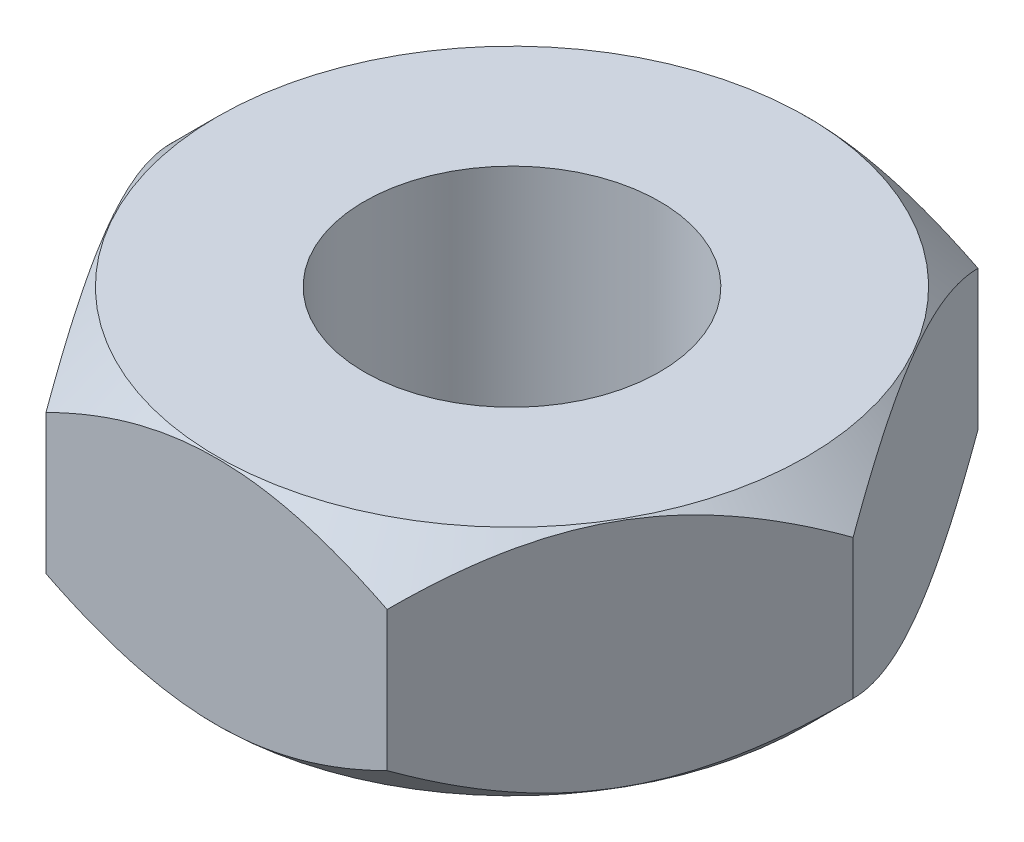
SolidWorks part; units mm, degrees
ref_plane "Alzado" through (0, 0, 0) normal (0, 0, 1) x (1, 0, 0)
ref_plane "Planta" through (0, 0, 0) normal (0, 1, 0) x (1, 0, 0)
ref_plane "Vista lateral" through (0, 0, 0) normal (1, 0, 0) x (0, 0, -1)
sketch "Croquis1" plane through (0, 0, 0) normal (0, 1, 0) x (1, 0, 0)
  line L1 (-7.3323, -12.7) -> (7.3323, -12.7)
  line L2 (7.3323, -12.7) -> (14.6647, 0)
  line L3 (14.6647, 0) -> (7.3323, 12.7)
  line L4 (7.3323, 12.7) -> (-7.3323, 12.7)
  line L5 (-7.3323, 12.7) -> (-14.6647, 0)
  line L6 (-14.6647, 0) -> (-7.3323, -12.7)
  circle A0 centre (0, 0) radius 12.7 construction
  circle A1 centre (0, 0) radius 6.35
  dimension "D2" = 12.7
  dimension "D1" = 25.4
extrude "Saliente-Extruir1" add sketch "Croquis1" along normal blind 10
sketch "Croquis2" plane through (0, 0, 0) normal (0, 0, 1) x (1, 0, 0)
  line L0 (-14.6647, 8) -> (-12.6647, 10)
  line L1 (-14.6647, 10) -> (-14.6647, 0) construction
  line L2 (-14.6647, 10) -> (-7.3323, 10) construction
  line L3 (-12.6647, 10) -> (-14.6647, 10)
  line L4 (-14.6647, 10) -> (-14.6647, 8)
  line L5 (0, 0) -> (0, 10) construction
  line L6 (-7.3323, 10) -> (7.3323, 10) construction
  dimension "D1" = 45
  dimension "D2" = 2
revolve "Cortar-Revolución1" cut sketch "Croquis2" angle 360 about L5
sketch "Croquis3" plane through (10.9985, 0, 6.35) normal (0.866, 0, 0.5) x (0.5, 0, -0.866)
  line L0 (0, 0) -> (0, 5) construction
  line L1 (-7.3323, 0) -> (7.3323, 0) construction
  dimension "D1" = 5
ref_plane "Plano1" through (0, 5, 0) normal (0, 1, 0) x (1, 0, 0)
mirror "Simetría1" about plane through (0, 5, 0) normal (0, 1, 0) of "Cortar-Revolución1"
